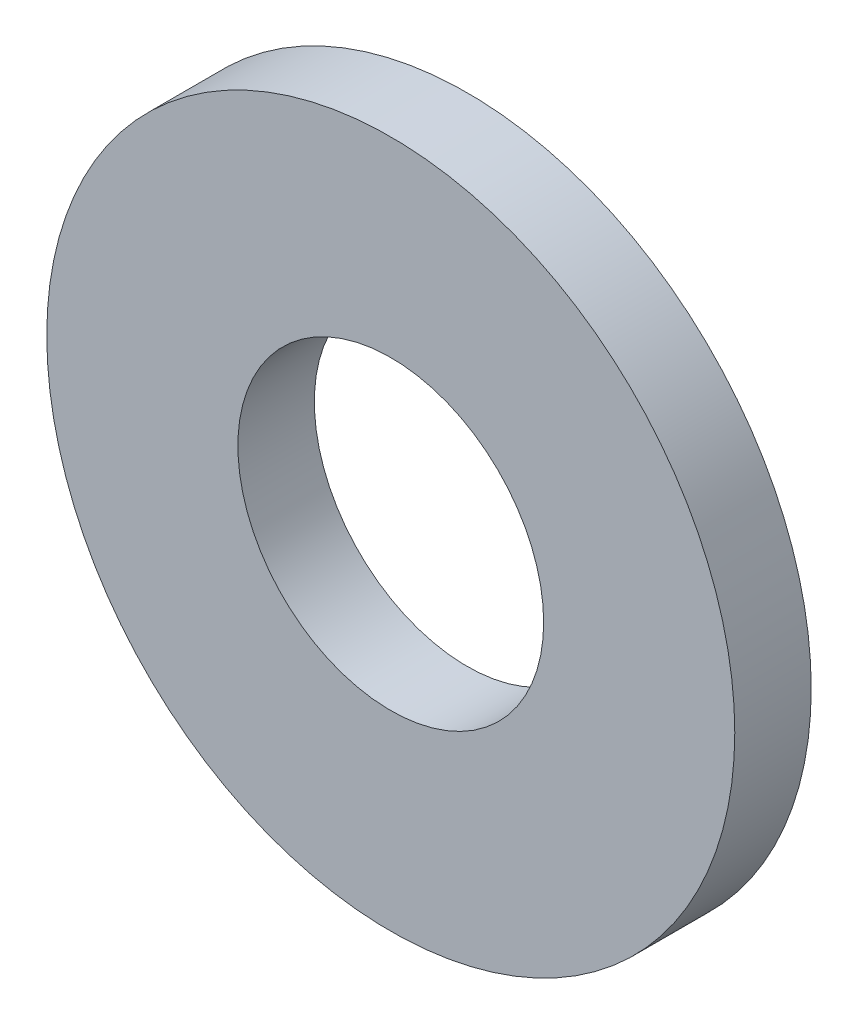
SolidWorks part; units mm, degrees
material "Plain Carbon Steel"
ref_plane "Front Plane" through (0, 0, 0) normal (0, 0, 1) x (1, 0, 0)
ref_plane "Top Plane" through (0, 0, 0) normal (0, 1, 0) x (1, 0, 0)
ref_plane "Right Plane" through (0, 0, 0) normal (1, 0, 0) x (0, 0, -1)
sketch "Sketch1" plane through (0, 0, 0) normal (0, 0, 1) x (1, 0, 0)
  circle A0 centre (0, 0) radius 7.1438
  circle A1 centre (0, 0) radius 3.175
extrude "Boss-Extrude1" add sketch "Sketch1" along normal blind 1.5875
